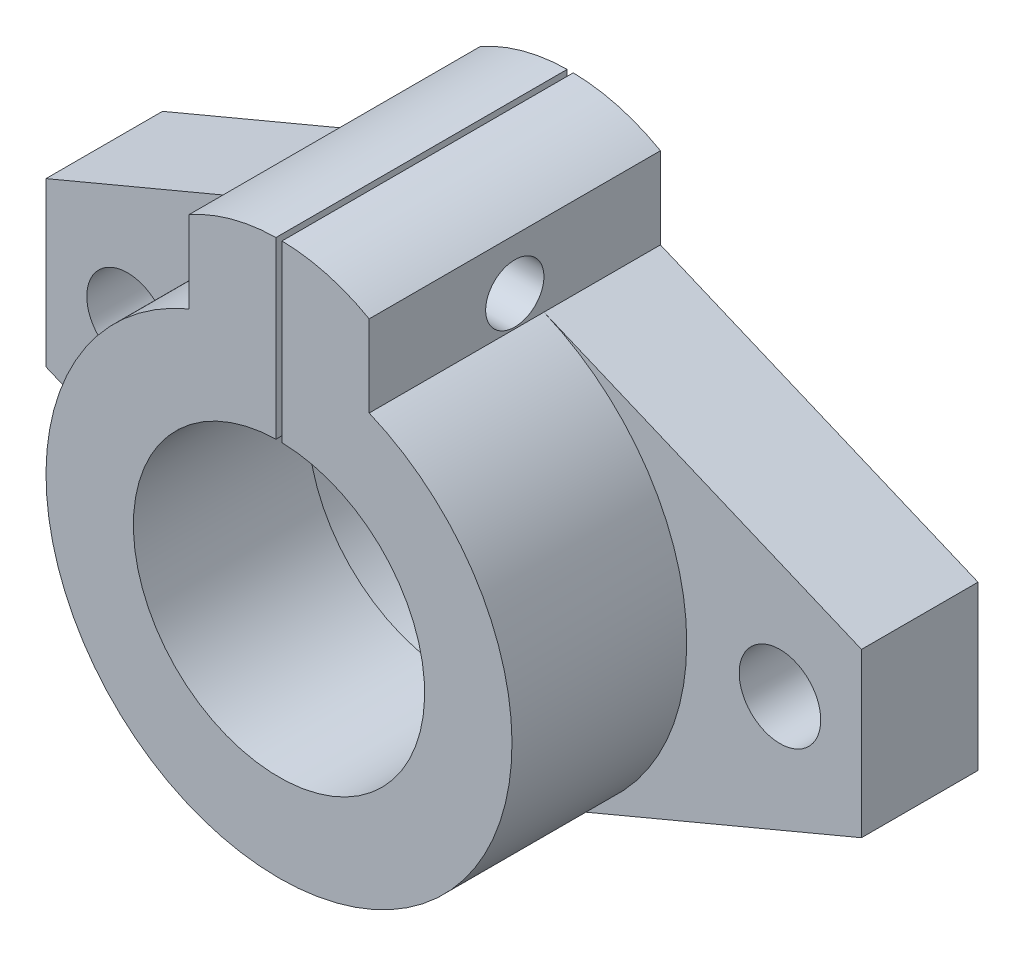
SolidWorks part; units mm, degrees
material "6061 合金"
ref_plane "前视基准面" through (0, 0, 0) normal (0, 0, 1) x (1, 0, 0)
ref_plane "上视基准面" through (0, 0, 0) normal (0, 1, 0) x (1, 0, 0)
ref_plane "右视基准面" through (0, 0, 0) normal (1, 0, 0) x (0, 0, -1)
sketch "草图1" plane through (0, 0, 0) normal (0, 0, 1) x (1, 0, 0)
  line L0 (-7.7403, 18.4415) -> (-7.7403, 25.4415)
  line L1 (-35, -7) -> (-35, 7)
  line L2 (-35, 7) -> (-7.7403, 18.4415)
  line L3 (-35, -7) -> (-7.7403, -18.4415)
  line L4 (7.7403, 18.4415) -> (7.7403, 25.4415)
  line L5 (35, -7) -> (7.7403, -18.4415)
  line L6 (35, -7) -> (35, 7)
  line L7 (35, 7) -> (7.7403, 18.4415)
  line L8 (0, 0) -> (-28, 0) construction
  circle A0 centre (0, 0) radius 13
  arc A1 (-7.7403, 18.4415) -> (7.7403, 18.4415) centre (0, 0) ccw
  arc A2 (-7.7403, 25.4415) -> (7.7403, 25.4415) centre (0, 11.8749) cw
  circle A3 centre (-28, 0) radius 3.5
  circle A4 centre (28, 0) radius 3.5
  dimension "D1" = 28
  dimension "D3" = 26
  dimension "D4" = 20
  dimension "D5" = 7
  dimension "D6" = 7
  dimension "D2" = 28
  dimension "D7" = 70
extrude "凸台-拉伸2" add sketch "草图1" along normal blind 10 contours A1 L5 L6 L7 | A2 L0 A1 L4 A0 | A1 L2 L1 L3
sketch "草图2" plane through (0, 0, 10) normal (0, 0, 1) x (1, 0, 0)
  line L0 (-7.7403, 18.4415) -> (-7.7403, 25.4415)
  line L1 (7.7403, 18.4415) -> (7.7403, 25.4415)
  circle A0 centre (0, 0) radius 12.5
  arc A1 (-7.7403, 18.4415) -> (7.7403, 18.4415) centre (0, 0) ccw
  arc A2 (-7.7403, 25.4415) -> (7.7403, 25.4415) centre (0, 11.8749) cw
extrude "凸台-拉伸3" add sketch "草图2" along normal blind 15
sketch "草图3" plane through (0, 0, 25) normal (0, 0, 1) x (1, 0, 0)
  line L1 (-0.2586, 12.3781) -> (-0.2586, 31.1043)
  line L2 (0.2586, 12.3781) -> (0.2586, 31.1043)
  line L3 (-0.2586, 12.3781) -> (0.2586, 12.3781)
  line L4 (-0.2586, 31.1043) -> (0.2586, 31.1043)
extrude "切除-拉伸1" cut sketch "草图3" against normal through all
sketch "草图4" plane through (7.7403, 0, 0) normal (1, 0, 0) x (0, 0, -1)
  circle A0 centre (-12.5, 21.0864) radius 2.5
extrude "切除-拉伸2" cut sketch "草图4" against normal through all
